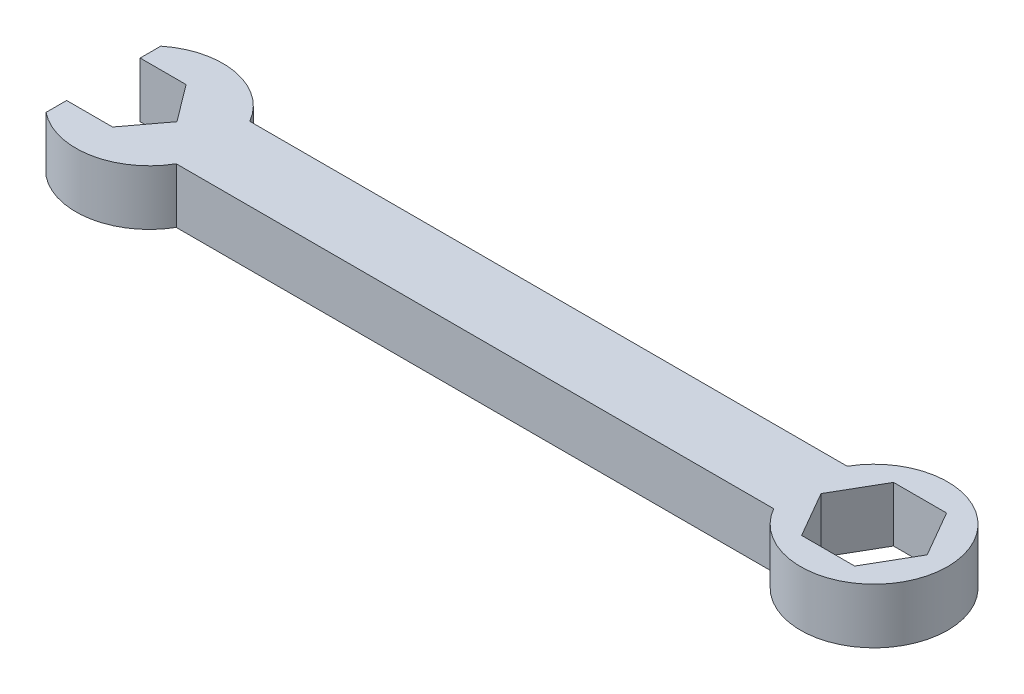
SolidWorks part; units mm, degrees
ref_plane "Front Plane" through (0, 0, 0) normal (0, 0, 1) x (1, 0, 0)
ref_plane "Top Plane" through (0, 0, 0) normal (0, 1, 0) x (1, 0, 0)
ref_plane "Right Plane" through (0, 0, 0) normal (1, 0, 0) x (0, 0, -1)
sketch "Sketch2" plane through (0, 0, 0) normal (0, 1, 0) x (1, 0, 0)
  line L0 (-46.2638, 0) -> (-50.0738, 5.08)
  line L1 (-41.275, -5.08) -> (41.275, -5.08)
  line L3 (-41.275, 5.08) -> (41.275, 5.08)
  line L5 (-41.275, -5.08) -> (41.275, 5.08) construction
  line L6 (-41.275, 5.08) -> (41.275, -5.08) construction
  line L7 (-56.4238, -5.08) -> (-50.0738, -5.08)
  line L9 (-56.4238, 5.08) -> (-50.0738, 5.08)
  line L11 (-56.4238, -5.08) -> (-56.4238, -7.9311)
  line L12 (-56.4238, -7.9311) -> (-56.4238, -5.08)
  line L13 (-56.4238, 5.08) -> (-56.4238, 7.9311)
  line L14 (-46.2638, 0) -> (-50.0738, -5.08)
  line L20 (57.4062, 0) -> (53.74, 6.35)
  line L21 (53.74, 6.35) -> (46.4076, 6.35)
  line L22 (46.4076, 6.35) -> (42.7415, 0)
  line L23 (42.7415, 0) -> (46.4076, -6.35)
  line L24 (46.4076, -6.35) -> (53.74, -6.35)
  line L25 (53.74, -6.35) -> (57.4062, 0)
  arc A0 (-56.4238, -7.9311) -> (-41.275, -5.08) centre (-50.0738, 0) ccw
  arc A1 (41.275, -5.08) -> (41.275, 5.08) centre (50.0738, 0) ccw
  arc A2 (-41.275, 5.08) -> (-56.4238, 7.9311) centre (-50.0738, 0) ccw
  circle A3 centre (50.0738, 0) radius 6.35 construction
  point P0 (0, 0)
  point P10 (-51.3438, 0)
  dimension "D3" = 20.32
  dimension "D4" = 20.32
  dimension "D1" = 82.55
  dimension "D2" = 10.16
  dimension "D5" = 12.7
  dimension "D7" = 6.35
extrude "Boss-Extrude1" add sketch "Sketch2" along normal blind 7.62 contours L3 A2 L13 L9 L0 L14 L7 L11 A0 L1 A1 L25 L24 L23 L22 L21 L20
